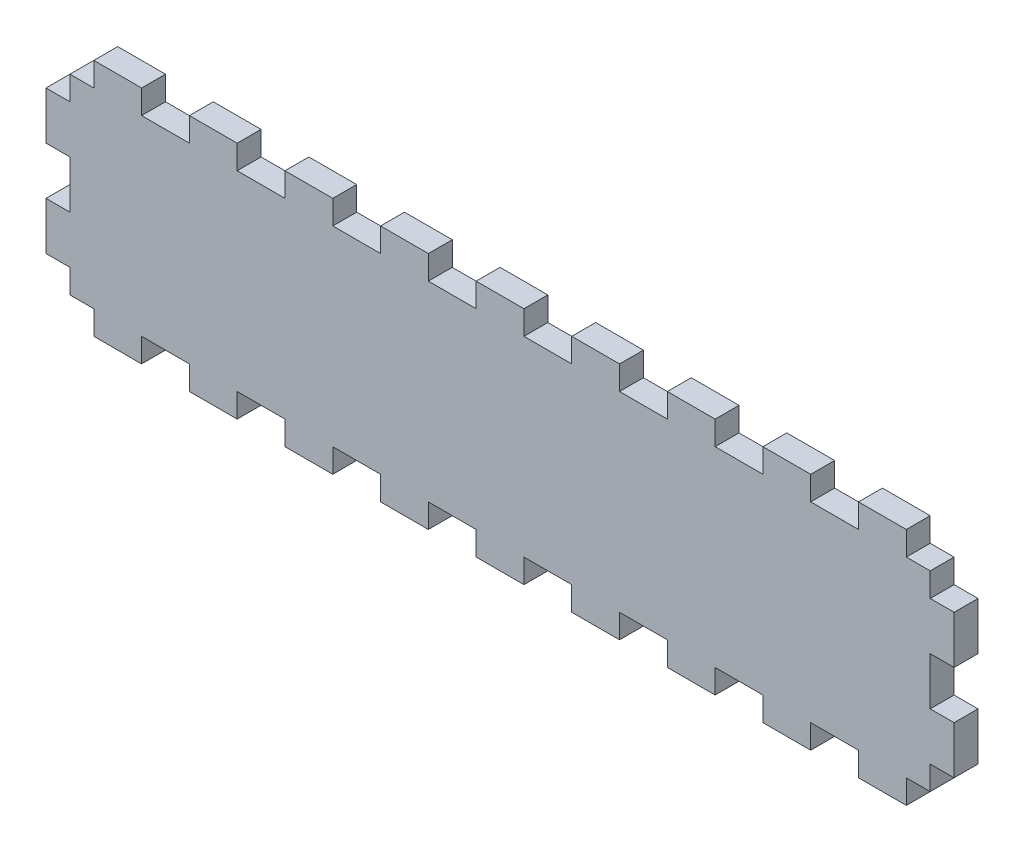
SolidWorks part; units mm, degrees
material "Pine"
ref_plane "Front Plane" through (0, 0, 0) normal (0, 0, 1) x (1, 0, 0)
ref_plane "Top Plane" through (0, 0, 0) normal (0, 1, 0) x (1, 0, 0)
ref_plane "Right Plane" through (0, 0, 0) normal (1, 0, 0) x (0, 0, -1)
sketch "Sketch2" plane through (0, 0, 0) normal (0, 0, 1) x (1, 0, 0)
  line L1 (0, 0) -> (241.3, 0)
  line L2 (0, 0) -> (0, 63.5)
  line L3 (0, 63.5) -> (241.3, 63.5)
  line L4 (241.3, 0) -> (241.3, 63.5)
  dimension "D1" = 63.5
  dimension "D2" = 241.3
extrude "Boss-Extrude1" add sketch "Sketch2" along normal blind 6.35
sketch "Sketch3" plane through (0, 0, 6.35) normal (0, 0, 1) x (1, 0, 0)
  line L1 (0, 63.5) -> (6.35, 63.5)
  line L2 (0, 63.5) -> (0, 50.8)
  line L3 (0, 50.8) -> (6.35, 50.8)
  line L4 (6.35, 63.5) -> (6.35, 50.8)
  line L5 (241.3, 63.5) -> (234.95, 63.5)
  line L6 (241.3, 63.5) -> (241.3, 50.8)
  line L7 (241.3, 50.8) -> (234.95, 50.8)
  line L8 (234.95, 63.5) -> (234.95, 50.8)
  dimension "D1" = 12.7
  dimension "D2" = 6.35
extrude "Cut-Extrude1" cut sketch "Sketch3" against normal through all
pattern_linear "LPattern1" count 3 spacing 25.4 along (0, -1, 0) of "Cut-Extrude1"
sketch "Sketch4" plane through (0, 0, 6.35) normal (0, 0, 1) x (1, 0, 0)
  line L0 (234.95, 63.5) -> (6.35, 63.5) construction
  line L1 (12.7, 63.5) -> (0, 63.5)
  line L2 (12.7, 63.5) -> (12.7, 57.15)
  line L3 (12.7, 57.15) -> (0, 57.15)
  line L4 (0, 63.5) -> (0, 57.15)
  line L5 (6.35, 0) -> (234.95, 0) construction
  line L6 (12.7, 0) -> (0, 0)
  line L7 (12.7, 0) -> (12.7, 6.35)
  line L8 (12.7, 6.35) -> (0, 6.35)
  line L9 (0, 0) -> (0, 6.35)
  line L10 (6.35, 50.8) -> (6.35, 63.5) construction
  dimension "D1" = 6.35
  dimension "D2" = 12.7
  dimension "D3" = 6.35
extrude "Cut-Extrude2" cut sketch "Sketch4" against normal through all
pattern_linear "LPattern2" count 10 spacing 25.4 along (1, 0, 0) of "Cut-Extrude2"
